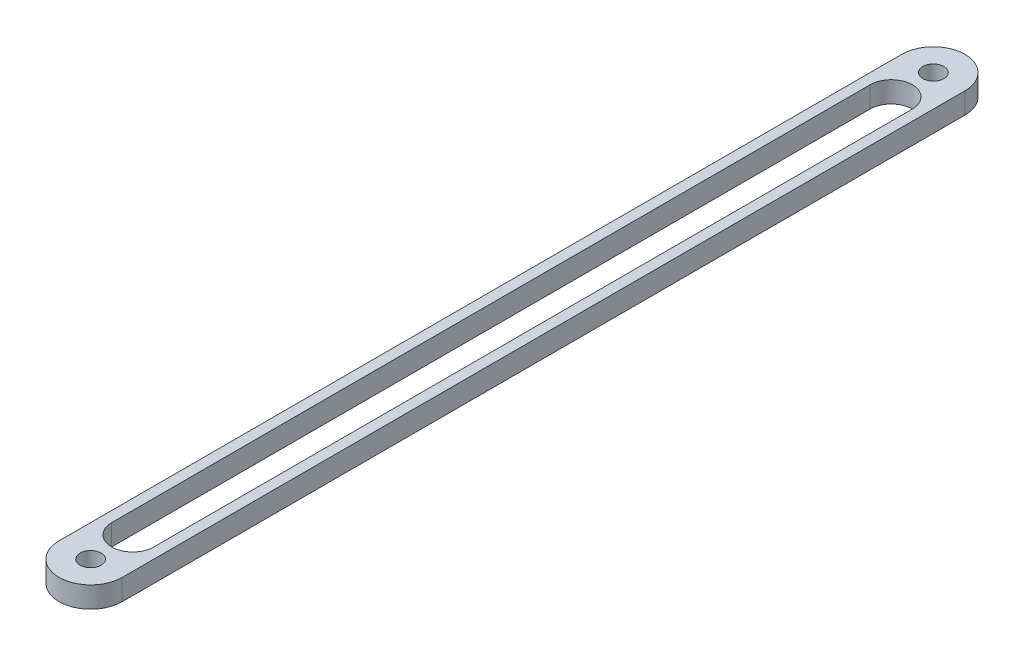
SolidWorks part; units mm, degrees
ref_plane "Front Plane" through (0, 0, 0) normal (0, 0, 1) x (1, 0, 0)
ref_plane "Top Plane" through (0, 0, 0) normal (0, 1, 0) x (1, 0, 0)
ref_plane "Right Plane" through (0, 0, 0) normal (1, 0, 0) x (0, 0, -1)
sketch "Sketch1" plane through (0, 0, 0) normal (0, 1, 0) x (1, 0, 0)
  line L0 (0, 0) -> (0, 100)
  line L1 (7.5, 100) -> (7.5, 0)
  line L2 (1.25, 95) -> (1.25, 5)
  line L3 (6.25, 5) -> (6.25, 95)
  arc A0 (0, 100) -> (7.5, 100) centre (3.75, 100) cw
  arc A1 (7.5, 0) -> (0, 0) centre (3.75, 0) cw
  circle A2 centre (3.75, 0) radius 1.25
  arc A3 (1.25, 95) -> (6.25, 95) centre (3.75, 95) cw
  arc A4 (1.25, 5) -> (6.25, 5) centre (3.75, 5) ccw
  circle A5 centre (3.75, 100) radius 1.25
  dimension "D1" = 3.75
  dimension "D3" = 2.5
  dimension "D6" = 2.5
  dimension "D7" = 2.5
  dimension "D2" = 100
  dimension "D4" = 90
  dimension "D5" = 5
extrude "Boss-Extrude1" add sketch "Sketch1" along normal blind 2.5
